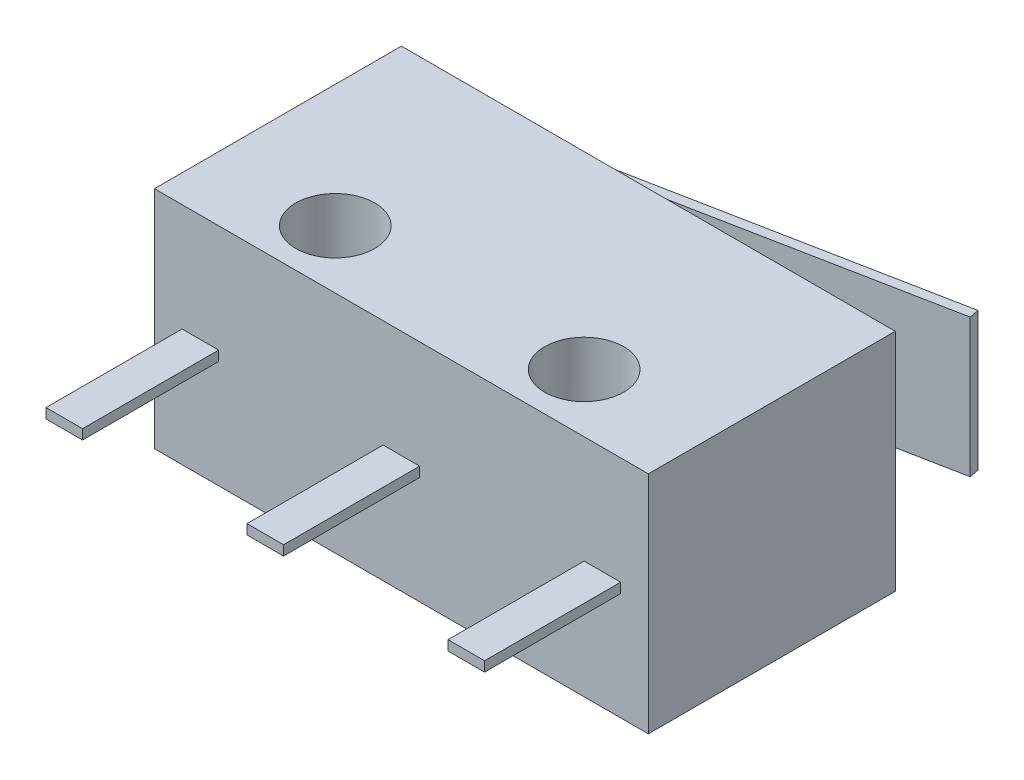
SolidWorks part; units mm, degrees
ref_plane "Front Plane" through (0, 0, 0) normal (0, 0, 1) x (1, 0, 0)
ref_plane "Top Plane" through (0, 0, 0) normal (0, 1, 0) x (1, 0, 0)
ref_plane "Right Plane" through (0, 0, 0) normal (1, 0, 0) x (0, 0, -1)
sketch "Sketch1" plane through (0, 0, 0) normal (0, 1, 0) x (1, 0, 0)
  line L1 (-6.35, -3.175) -> (6.35, -3.175)
  line L2 (-6.35, -3.175) -> (-6.35, 3.175)
  line L3 (-6.35, 3.175) -> (6.35, 3.175)
  line L4 (6.35, -3.175) -> (6.35, 3.175)
  line L5 (-6.35, -3.175) -> (6.35, 3.175) construction
  line L6 (-6.35, 3.175) -> (6.35, -3.175) construction
  point P0 (0, 0)
  dimension "D1" = 12.7
  dimension "D2" = 6.35
extrude "Boss-Extrude1" add sketch "Sketch1" along normal blind 5.7912
sketch "Sketch2" plane through (0, 5.7912, 0) normal (0, 1, 0) x (1, 0, 0)
  line L0 (0, 3.175) -> (0, -3.175) construction
  line L1 (6.35, 3.175) -> (-6.35, 3.175) construction
  line L2 (-6.35, -3.175) -> (6.35, -3.175) construction
  line L3 (6.35, -3.175) -> (6.35, 3.175) construction
  circle A0 centre (3.2, -1.675) radius 1.016
  circle A1 centre (-3.2, -1.675) radius 1.016
  dimension "D2" = 2.032
  dimension "D1" = 3.15
  dimension "D3" = 1.5
extrude "Cut-Extrude1" cut sketch "Sketch2" against normal up to surface (5.7912 mm away) up to face at (0, 0, 0)
ref_plane "Plane1" through (0, 4.6736, 0) normal (0, 1, 0) x (1, 0, 0)
ref_plane "Plane2" through (0, 1.1176, 0) normal (0, -1, 0) x (-1, 0, 0)
sketch "Sketch3" plane through (0, 4.6736, 0) normal (0, 1, 0) x (1, 0, 0)
  line L0 (6.35, 3.175) -> (-6.35, 3.175) construction
  line L1 (-6.35, 3.175) -> (-6.35, -3.175) construction
  line L2 (-3.1496, 3.175) -> (-1.6256, 3.175)
  arc A0 (-3.1496, 3.175) -> (-1.6256, 3.175) centre (-2.3876, 3.175) cw
  dimension "D2" = 0.762
  dimension "D1" = 3.9624
extrude "Boss-Extrude2" add sketch "Sketch3" against normal up to surface (3.556 mm away) contours A0 L2 up to plane "Plane2"
ref_plane "Plane3" through (-0.834, 0, -4.2559) normal (-0.1923, 0, -0.9813) x (-0.9813, 0, 0.1923)
sketch "Sketch4" plane through (-0.834, 0, -4.2559) normal (-0.1923, 0, -0.9813) x (-0.9813, 0, 0.1923)
  line L0 (5.6209, 5.7912) -> (5.6209, 0) construction
  line L1 (5.6209, 4.6736) -> (-6.8421, 4.6736)
  line L2 (5.6209, 4.6736) -> (5.6209, 1.1176)
  line L3 (5.6209, 1.1176) -> (-6.8421, 1.1176)
  line L4 (-6.8421, 4.6736) -> (-6.8421, 1.1176)
  line L5 (-6.8421, 5.7912) -> (5.6209, 5.7912) construction
  line L6 (-6.8421, 0) -> (5.6209, 0) construction
  line L7 (-6.8421, 5.7912) -> (-6.8421, 0) construction
  dimension "D1" = 1.1176
  dimension "D2" = 1.1176
extrude "Boss-Extrude3" add sketch "Sketch4" along normal blind 0.254 separate body
sketch "Sketch5" plane through (0, 0, 3.175) normal (0, 0, 1) x (1, 0, 0)
  line L0 (-5.6388, 2.8956) -> (-6.35, 2.8956) construction
  line L1 (-5.6388, 3.0226) -> (-4.699, 3.0226)
  line L2 (-5.6388, 3.0226) -> (-5.6388, 2.7686)
  line L3 (-5.6388, 2.7686) -> (-4.699, 2.7686)
  line L4 (-4.699, 3.0226) -> (-4.699, 2.7686)
  line L5 (-0.4699, 3.0226) -> (0.4699, 3.0226)
  line L6 (-0.4699, 3.0226) -> (-0.4699, 2.7686)
  line L7 (-0.4699, 2.7686) -> (0.4699, 2.7686)
  line L8 (0.4699, 3.0226) -> (0.4699, 2.7686)
  line L9 (4.699, 3.0226) -> (5.6388, 3.0226)
  line L10 (4.699, 3.0226) -> (4.699, 2.7686)
  line L11 (4.699, 2.7686) -> (5.6388, 2.7686)
  line L12 (5.6388, 3.0226) -> (5.6388, 2.7686)
  line L13 (-6.35, 5.7912) -> (-6.35, 0) construction
  line L14 (5.6388, 2.8956) -> (6.35, 2.8956) construction
  line L15 (6.35, 5.7912) -> (6.35, 0) construction
  line L16 (-4.699, 2.8956) -> (-0.4699, 2.8956) construction
  line L17 (0.4699, 2.8956) -> (4.699, 2.8956) construction
  dimension "D1" = 0.9398
  dimension "D2" = 0.254
  dimension "D3" = 0.7112
extrude "Boss-Extrude4" add sketch "Sketch5" along normal blind 3.5
